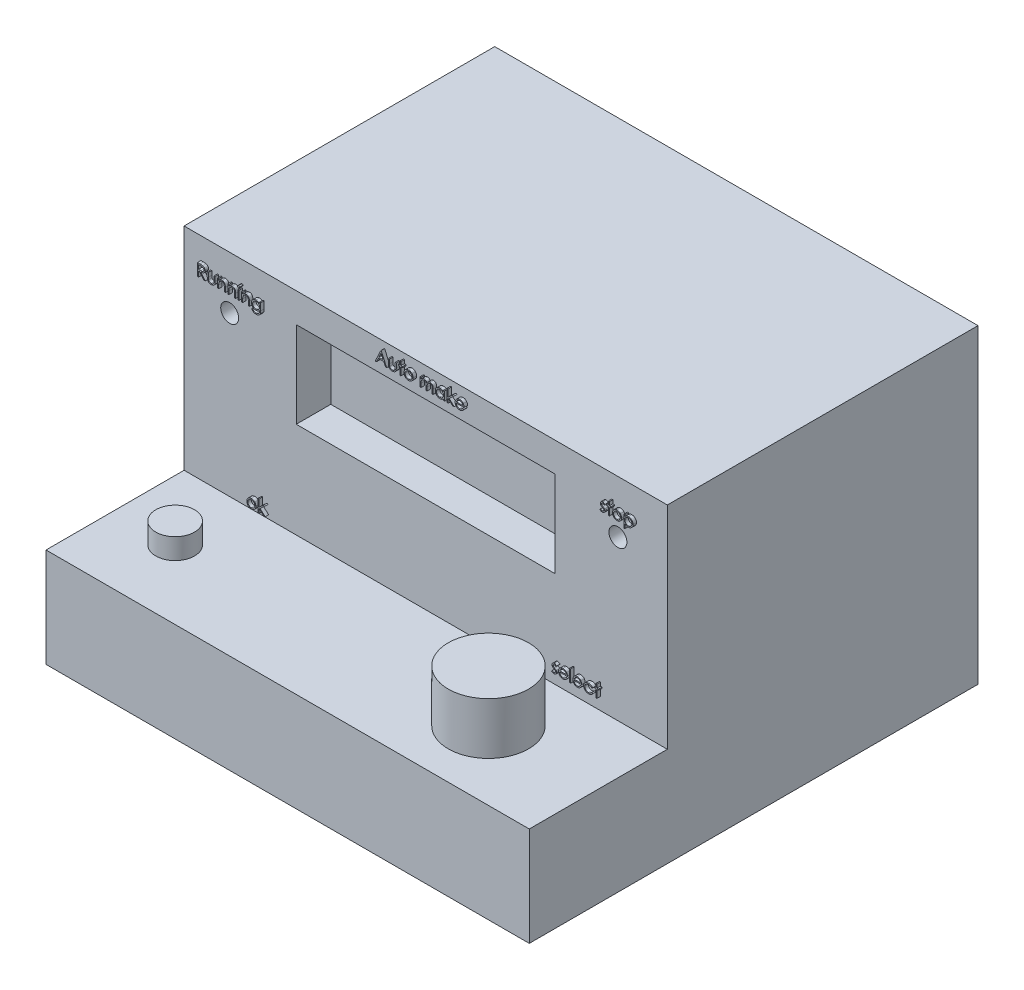
SolidWorks part; units mm, degrees
ref_plane "Front Plane" through (0, 0, 0) normal (0, 0, 1) x (1, 0, 0)
ref_plane "Top Plane" through (0, 0, 0) normal (0, 1, 0) x (1, 0, 0)
ref_plane "Right Plane" through (0, 0, 0) normal (1, 0, 0) x (0, 0, -1)
sketch "Sketch1" plane through (0, 0, 0) normal (0, 0, 1) x (1, 0, 0)
  line L1 (-70, 45) -> (70, 45)
  line L2 (-70, 45) -> (-70, -45)
  line L3 (-70, -45) -> (70, -45)
  line L4 (70, 45) -> (70, -45)
  line L5 (-70, 45) -> (70, -45) construction
  line L6 (-70, -45) -> (70, 45) construction
  point P0 (0, 0)
  dimension "D1" = 90
  dimension "D2" = 140
extrude "Boss-Extrude4" add sketch "Sketch1" along normal mid plane 90 contours L1 L4 L3 L2
sketch "Sketch2" plane through (0, 0, 45) normal (0, 0, 1) x (1, 0, 0)
  line L0 (-70, 45) -> (-70, -45) construction
  line L1 (-37.5, 36.4987) -> (37.5, 36.4987)
  line L2 (-37.5, 36.4987) -> (-37.5, 11.4987)
  line L3 (-37.5, 11.4987) -> (37.5, 11.4987)
  line L4 (37.5, 36.4987) -> (37.5, 11.4987)
  line L6 (70, 45) -> (70, -45) construction
  dimension "D1" = 75
  dimension "D2" = 25
  dimension "D3" = 32.5
  dimension "D4" = 32.5
extrude "Cut-Extrude1" cut sketch "Sketch2" against normal blind 10 contours L2 L3 L4 L1
sketch "Sketch7" plane through (0, 0, 45) normal (0, 0, 1) x (1, 0, 0)
  circle A0 centre (-56.7825, 29.7685) radius 2.6004
  circle A1 centre (55.6773, 29.7685) radius 2.6004
extrude "Cut-Extrude3" cut sketch "Sketch7" against normal blind 10
sketch "Sketch8" plane through (0, 0, -45) normal (0, 0, -1) x (-1, 0, 0)
  circle A0 centre (-43.0083, -20.0553) radius 17.9817
extrude "Cut-Extrude4" cut sketch "Sketch8" against normal blind 5
sketch "Sketch9" plane through (0, 0, -40) normal (0, 0, -1) x (-1, 0, 0)
  circle A0 centre (-51.1441, -19.6191) radius 2
  circle A2 centre (-37.1542, -19.0868) radius 2
  dimension "D1" = 4
  dimension "D2" = 14
extrude "Cut-Extrude5" cut sketch "Sketch9" against normal blind 23
mirror "Mirror1" about plane through (0, 0, 0) normal (1, 0, 0) of "Cut-Extrude4", "Cut-Extrude5"
sketch "Sketch11" plane through (0, 0, 45) normal (0, 0, 1) x (1, 0, 0)
  text T0 "ok"
  text T1 "select"
  text T2 "Auto make"
  text T3 "Running"
  text T4 "stop"
extrude "Boss-Extrude7" add sketch "Sketch11" along normal blind 1
sketch "Sketch13" plane through (0, 0, -45) normal (0, 0, -1) x (-1, 0, 0)
  text T0 "IN"
  text T1 "OUT"
extrude "Boss-Extrude8" add sketch "Sketch13" along normal blind 1
sketch "Sketch14" plane through (0, 0, 45) normal (0, 0, 1) x (1, 0, 0)
  line L0 (70, 45) -> (70, -45) construction
  line L1 (-70, -45) -> (70, -45)
  line L2 (-70, -45) -> (-70, -16.2927)
  line L3 (-70, -16.2927) -> (70, -16.2927)
  line L4 (70, -45) -> (70, -16.2927)
extrude "Boss-Extrude9" add sketch "Sketch14" along normal blind 60
sketch "Sketch15" plane through (0, 0, 105) normal (0, 0, 1) x (1, 0, 0)
  line L1 (-70, -16.2927) -> (70, -16.2927)
  line L2 (-70, -16.2927) -> (-70, -45)
  line L3 (-70, -45) -> (70, -45)
  line L4 (70, -16.2927) -> (70, -45)
extrude "Cut-Extrude6" cut sketch "Sketch15" against normal blind 20
sketch "Sketch16" plane through (0, -16.2927, 0) normal (0, 1, 0) x (1, 0, 0)
  line L0 (-70, -65) -> (70, -65) construction
  line L1 (-70, -85) -> (-70, -45) construction
  line L2 (70, -85) -> (70, -45) construction
  circle A0 centre (-52.5825, -65) radius 5.611
  circle A1 centre (38.1777, -65) radius 11.6315
extrude "Boss-Extrude11" add sketch "Sketch16" along normal blind 15
sketch "Sketch18" plane through (0, -1.2927, 0) normal (0, 1, 0) x (1, 0, 0)
  circle A0 centre (-52.5825, -65) radius 5.611
extrude "Cut-Extrude7" cut sketch "Sketch18" against normal blind 9
sketch "Sketch19" plane through (0, 0, -45) normal (0, 0, -1) x (-1, 0, 0)
  line L2 (-48.9889, 11.416) -> (-41.4521, 11.416)
  line L3 (-48.9889, 11.416) -> (-48.9889, 8.7559)
  line L4 (-48.9889, 8.7559) -> (-41.4521, 8.7559)
  line L5 (-41.4521, 11.416) -> (-41.4521, 8.7559)
extrude "Cut-Extrude8" cut sketch "Sketch19" against normal blind 1
